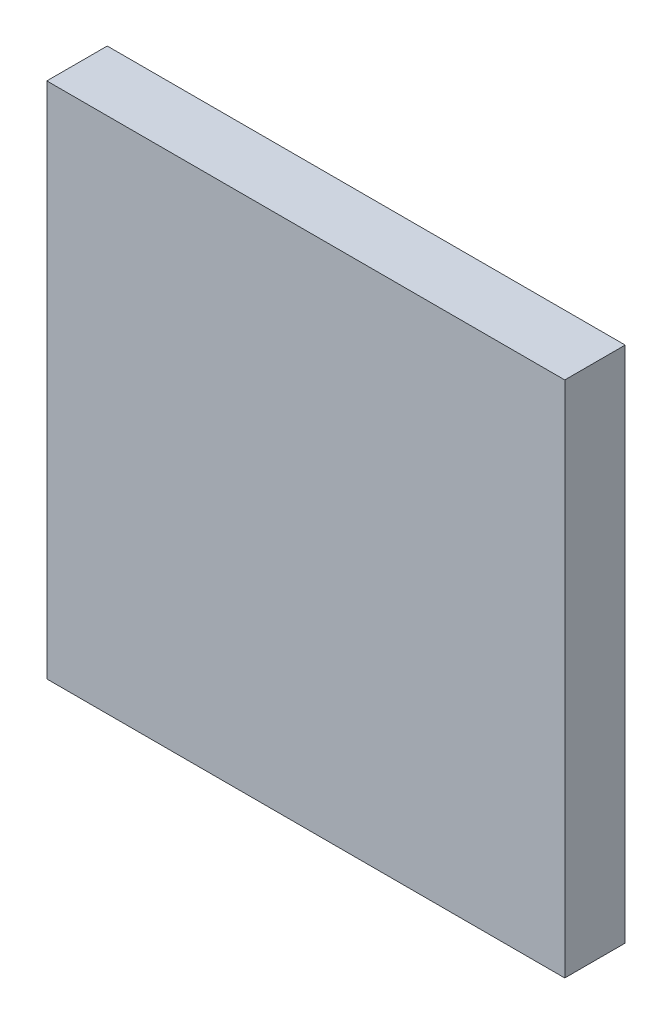
SolidWorks part; units mm, degrees
ref_plane "Front Plane" through (0, 0, 0) normal (0, 0, 1) x (1, 0, 0)
ref_plane "Top Plane" through (0, 0, 0) normal (0, 1, 0) x (1, 0, 0)
ref_plane "Right Plane" through (0, 0, 0) normal (1, 0, 0) x (0, 0, -1)
sketch "Sketch1" plane through (0, 0, 0) normal (0, 0, 1) x (1, 0, 0)
  line L1 (6, -6) -> (-6, -6)
  line L2 (6, -6) -> (6, 6)
  line L3 (6, 6) -> (-6, 6)
  line L4 (-6, -6) -> (-6, 6)
  line L5 (6, -6) -> (-6, 6) construction
  line L6 (6, 6) -> (-6, -6) construction
  point P0 (0, 0)
  dimension "D1" = 12
  dimension "D2" = 12
extrude "Boss-Extrude1" add sketch "Sketch1" along normal blind 1.4
